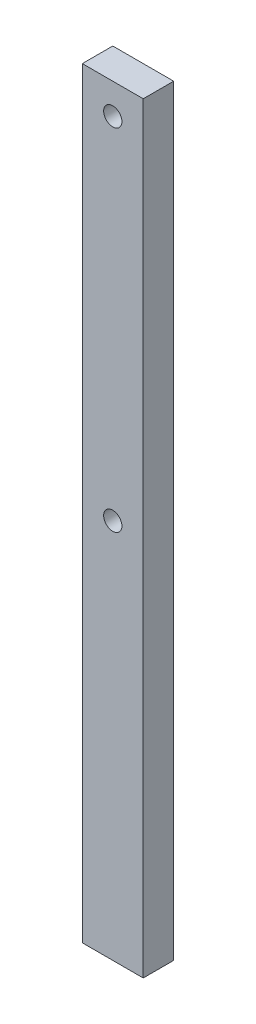
SolidWorks part; units mm, degrees
ref_plane "Front Plane" through (0, 0, 0) normal (0, 0, 1) x (1, 0, 0)
ref_plane "Top Plane" through (0, 0, 0) normal (0, 1, 0) x (1, 0, 0)
ref_plane "Right Plane" through (0, 0, 0) normal (1, 0, 0) x (0, 0, -1)
sketch "Sketch1" plane through (0, 0, 0) normal (0, 0, 1) x (1, 0, 0)
  line L1 (-10, -125) -> (10, -125)
  line L2 (-10, -125) -> (-10, 125)
  line L3 (-10, 125) -> (10, 125)
  line L4 (10, -125) -> (10, 125)
  line L5 (-10, -125) -> (10, 125) construction
  line L6 (-10, 125) -> (10, -125) construction
  point P0 (0, 0)
  dimension "D1" = 20
  dimension "D2" = 250
extrude "Boss-Extrude1" add sketch "Sketch1" along normal blind 10
sketch "Sketch2" plane through (0, 0, 10) normal (0, 0, 1) x (1, 0, 0)
  line L0 (10, 125) -> (-10, 125) construction
  circle A0 centre (0, 115) radius 3
  circle A1 centre (0, 0) radius 3
  dimension "D1" = 10
  dimension "D2" = 2
extrude "Cut-Extrude1" cut sketch "Sketch2" against normal up to surface (10 mm away) up to face at (0, 0, 0)
